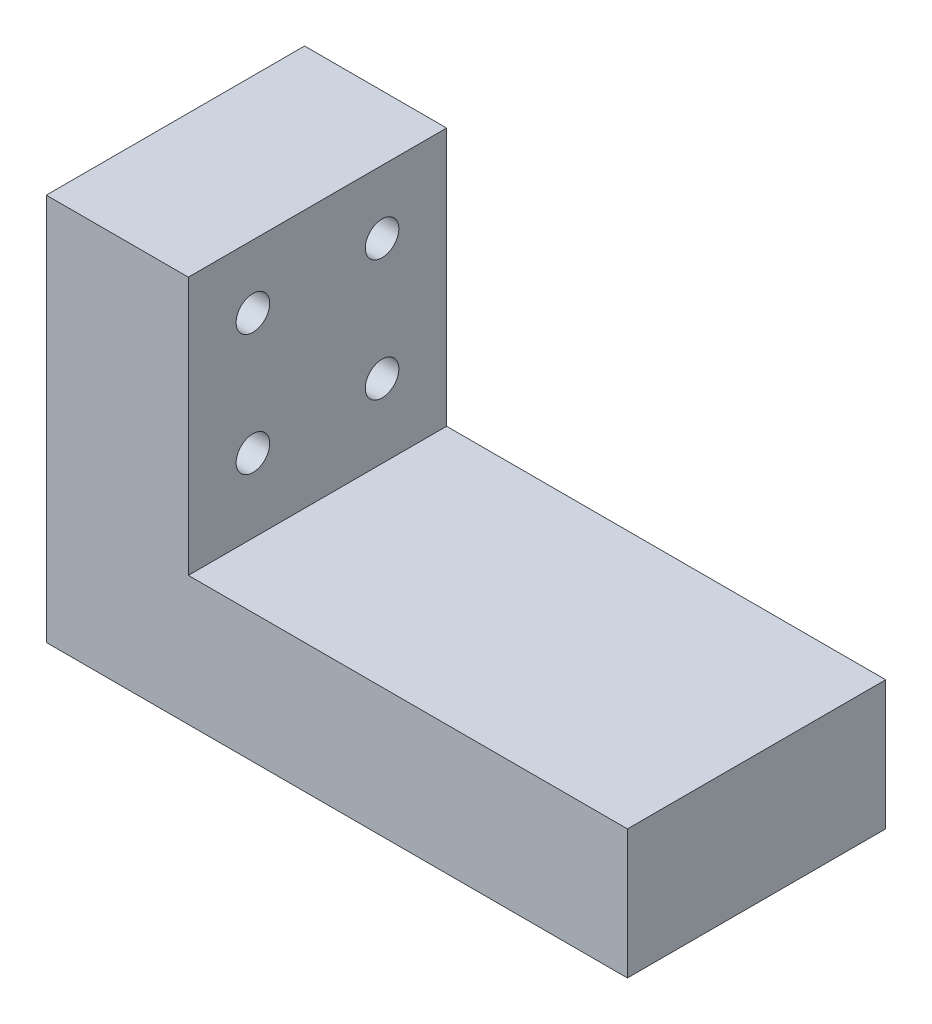
SolidWorks part; units mm, degrees
ref_plane "Plan de face" through (0, 0, 0) normal (0, 0, 1) x (1, 0, 0)
ref_plane "Plan de dessus" through (0, 0, 0) normal (0, 1, 0) x (1, 0, 0)
ref_plane "Plan de droite" through (0, 0, 0) normal (1, 0, 0) x (0, 0, -1)
sketch "Esquisse1" plane through (0, 0, 0) normal (0, 0, 1) x (1, 0, 0)
  line L0 (0, 0) -> (0, 30)
  line L1 (0, 30) -> (11, 30)
  line L8 (45, 10) -> (45, 0)
  line L9 (45, 0) -> (0, 0)
  line L12 (11, 30) -> (11, 10)
  line L14 (11, 10) -> (45, 10)
  dimension "D1" = 10
  dimension "D2" = 30
  dimension "D3" = 45
  dimension "D5" = 11
extrude "Boss.-Extru.1" add sketch "Esquisse1" along normal blind 20
sketch "Esquisse2" plane through (0, 0, 0) normal (0, -1, 0) x (1, 0, 0)
  line L0 (17.5, 10) -> (37.5, 10) construction
  line L2 (0, 20) -> (0, 0) construction
  line L3 (45, 20) -> (45, 0) construction
  circle A0 centre (17.5, 10) radius 2.8
  circle A1 centre (37.5, 10) radius 2.8
  point P11 (0, 10)
  dimension "D1" = 5.6
  dimension "D2" = 5.6
  dimension "D3" = 20
  dimension "D4" = 7.5
extrude "Enlèv. mat.-Extru.1" cut sketch "Esquisse2" against normal blind 8.1
sketch "Esquisse3" plane through (11, 0, 0) normal (1, 0, 0) x (0, 0, -1)
  line L0 (-20, 10) -> (0, 10) construction
  line L1 (-15, 25.1) -> (-5, 25.1) construction
  line L2 (-15, 25.1) -> (-15, 15.7) construction
  line L3 (-15, 15.7) -> (-5, 15.7) construction
  line L4 (-5, 25.1) -> (-5, 15.7) construction
  line L5 (-15, 25.1) -> (-5, 15.7) construction
  line L6 (-15, 15.7) -> (-5, 25.1) construction
  line L7 (-19, 29.8) -> (-1, 29.8) construction
  line L8 (-19, 29.8) -> (-19, 11) construction
  line L9 (-19, 11) -> (-1, 11) construction
  line L10 (-1, 29.8) -> (-1, 11) construction
  line L11 (-19, 29.8) -> (-1, 11) construction
  line L12 (-19, 11) -> (-1, 29.8) construction
  line L13 (-20, 30) -> (0, 30) construction
  circle A0 centre (-15, 25.1) radius 1.3
  circle A1 centre (-5, 25.1) radius 1.3
  circle A2 centre (-5, 15.7) radius 1.3
  circle A3 centre (-15, 15.7) radius 1.3
  point P0 (-10, 20.4)
  point P5 (-10, 20.4)
  point P15 (-10, 30)
  dimension "D6" = 2.6
  dimension "D1" = 10
  dimension "D2" = 9.4
  dimension "D3" = 18.8
  dimension "D4" = 18
  dimension "D5" = 1
  dimension "D7" = 2
  dimension "D8" = 2
extrude "Enlèv. mat.-Extru.2" cut sketch "Esquisse3" against normal up to next
equation "\"D2@Esquisse2\"=\"D1@Esquisse2\""
